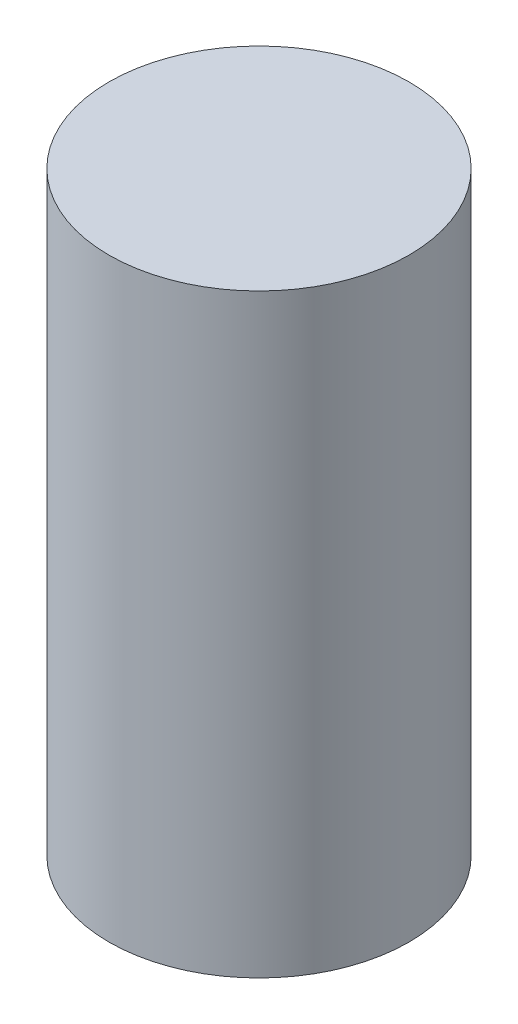
SolidWorks part; units mm, degrees
ref_plane "Спереди" through (0, 0, 0) normal (0, 0, 1) x (1, 0, 0)
ref_plane "Сверху" through (0, 0, 0) normal (0, 1, 0) x (1, 0, 0)
ref_plane "Справа" through (0, 0, 0) normal (1, 0, 0) x (0, 0, -1)
sketch "Эскиз1" plane through (0, 0, 0) normal (0, 1, 0) x (1, 0, 0)
  circle A0 centre (0, 0) radius 2.9
  dimension "D1" = 5.8
extrude "Бобышка-Вытянуть1" add sketch "Эскиз1" along normal blind 11.5
